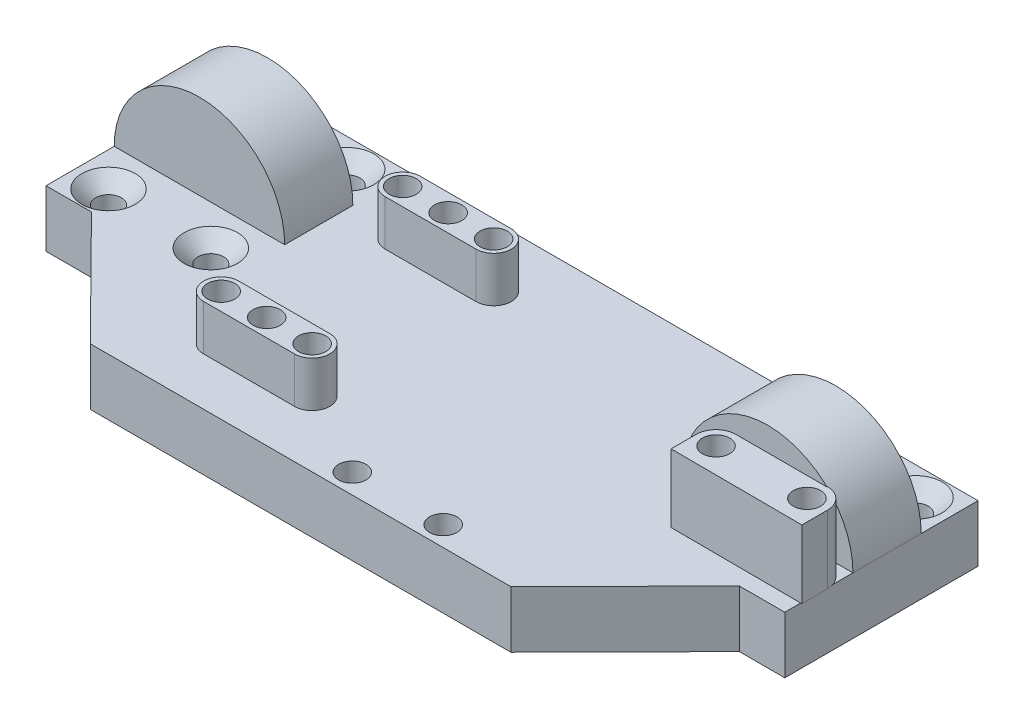
SolidWorks part; units mm, degrees
ref_plane "Front Plane" through (0, 0, 0) normal (0, 0, 1) x (1, 0, 0)
ref_plane "Top Plane" through (0, 0, 0) normal (0, 1, 0) x (1, 0, 0)
ref_plane "Right Plane" through (0, 0, 0) normal (1, 0, 0) x (0, 0, -1)
sketch "Sketch1" plane through (0, 0, 0) normal (0, 1, 0) x (1, 0, 0)
  point P0 (0, 0)
  line B0 (-64.8643, -10.474) -> (-34.8643, -10.474)
  line B1 (-34.8643, 23.526) -> (-34.8643, -10.474)
  line B2 (-64.8643, 23.526) -> (-64.8643, -10.474)
  line B3 (-64.8643, 23.526) -> (-34.8643, 23.526)
  circle B4 centre (-40.8643, -5.474) radius 2
  circle B5 centre (-58.8643, -5.474) radius 2
  circle B6 centre (-58.8643, 18.526) radius 2
  circle B7 centre (-40.8643, 18.526) radius 2
  line B8 (35.1357, -10.474) -> (65.1357, -10.474)
  line B9 (65.1357, 23.526) -> (65.1357, -10.474)
  line B10 (35.1357, 23.526) -> (35.1357, -10.474)
  line B11 (35.1357, 23.526) -> (65.1357, 23.526)
  circle B12 centre (59.1357, -5.474) radius 2
  circle B13 centre (41.1357, -5.474) radius 2
  circle B14 centre (41.1357, 18.526) radius 2
  circle B15 centre (59.1357, 18.526) radius 2
  line B16 (81.334, -15.2142) -> (81.234, -15.2142)
  line B17 (81.234, -15.2142) -> (81.234, -16.0085)
  line B18 (81.234, -16.0085) -> (81.334, -16.0085)
  line B19 (81.334, -16.0085) -> (81.334, -15.2142)
  line B20 (-6.166, 12.8273) -> (-6.266, 12.8273)
  line B21 (-6.266, 12.8273) -> (-6.266, -19.1727)
  line B22 (-6.266, -19.1727) -> (-6.166, -19.1727)
  line B23 (-6.166, -19.1727) -> (-6.166, 12.8273)
  line B24 (-6.266, -14.7727) -> (-15.766, -14.7727)
  line B25 (-15.866, -12.7727) -> (-17.766, -12.7727)
  line B26 (-17.766, -12.7727) -> (-17.766, -10.7727)
  line B27 (-17.766, -10.7727) -> (-17.766, 4.4273)
  line B28 (-17.766, 4.4273) -> (-17.766, 6.4273)
  line B29 (-15.766, 6.4273) -> (-15.766, 8.4273)
  line B30 (-15.866, 6.4273) -> (-17.766, 6.4273)
  line B31 (-6.266, 8.4273) -> (-15.766, 8.4273)
  line B32 (28.1, 4.7273) -> (33.234, 0.778)
  line B33 (33.234, 0.778) -> (33.234, -15.5313)
  line B34 (42.234, -7.5727) -> (42.234, -3.1727)
  line B35 (45.734, 0.3273) -> (61.734, 0.3273)
  line B36 (65.234, -3.1727) -> (65.234, -7.5727)
  line B37 (33.334, -7.6727) -> (73.6926, -7.6727)
  line B38 (73.6926, -7.6727) -> (81.234, -15.2142)
  line B39 (66.5698, -30.6727) -> (41.3754, -30.6727)
  line B40 (41.3754, -30.6727) -> (33.3754, -22.6727)
  line B41 (33.3754, -22.6727) -> (26.234, -22.6727)
  line B42 (25.334, -27.1727) -> (25.334, -22.7727)
  line B43 (5.734, -30.7727) -> (21.734, -30.7727)
  line B44 (2.234, -27.1727) -> (2.234, -22.7727)
  line B45 (-6.166, -22.7727) -> (1.634, -22.7727)
  line B46 (-6.166, -22.7727) -> (-6.166, -19.1727)
  line B47 (-6.166, 12.8273) -> (-6.166, 16.4273)
  line B48 (-6.166, 16.4273) -> (1.634, 16.4273)
  line B49 (1.634, 16.4273) -> (1.634, 12.8273)
  line B50 (17.7003, 12.7273) -> (27.4371, 5.3273)
  line B51 (-2.666, 12.7273) -> (17.7003, 12.7273)
  arc B52 (45.734, 0.3273) -> (42.234, -3.1727) centre (45.734, -3.1727) ccw
  arc B53 (65.334, -3.1727) -> (61.734, 0.4273) centre (61.734, -3.1727) ccw
  arc B54 (89.2916, -26.6217) -> (78.285, -15.6152) centre (77.734, -27.1727) ccw
  arc B55 (78.285, -38.7303) -> (89.2916, -27.7237) centre (77.734, -27.1727) ccw
  arc B56 (66.1764, -27.7237) -> (77.183, -38.7303) centre (77.734, -27.1727) ccw
  arc B57 (21.734, -30.7727) -> (25.334, -27.1727) centre (21.734, -27.1727) ccw
  arc B58 (2.234, -27.1727) -> (5.734, -30.6727) centre (5.734, -27.1727) ccw
  arc B59 (-6.266, -19.1727) -> (-2.666, -22.7727) centre (-2.666, -19.1727) ccw
  dimension "D1" = 130
sketch_block_instance "Block-LinearBearing-1"
sketch_block "Block-LinearBearing"
sketch_block_instance "Block-LinearBearing-2"
sketch_block_instance "Block-LARGERMOTORSIDE-1"
sketch_block "Block-LARGERMOTORSIDE"
sketch "Sketch2" plane through (0, 0, 0) normal (0, 1, 0) x (1, 0, 0)
  line L0 (35.1357, -10.474) -> (65.1357, -10.474) construction
  line L1 (65.1357, 23.526) -> (65.1357, -10.474) construction
  line L2 (35.1357, 23.526) -> (65.1357, 23.526) construction
  line L3 (-64.8643, -10.474) -> (-34.8643, -10.474) construction
  line L4 (-64.8643, 23.526) -> (-34.8643, 23.526) construction
  line L5 (-64.8643, 23.526) -> (-64.8643, -10.474) construction
  line L6 (35.1357, -10.474) -> (65.1357, -10.474)
  line L7 (65.1357, 23.526) -> (65.1357, -10.474)
  line L8 (35.1357, 23.526) -> (65.1357, 23.526)
  line L9 (-64.8643, -10.474) -> (-34.8643, -10.474)
  line L10 (-64.8643, 23.526) -> (-34.8643, 23.526)
  line L11 (-64.8643, 23.526) -> (-64.8643, -10.474)
  line L12 (-34.8643, 23.526) -> (35.1357, 23.526)
  line L13 (-34.8643, -10.474) -> (35.1357, -10.474)
  line L14 (-17.766, -12.7727) -> (-17.766, -30.6727)
  line L15 (-17.766, -30.6727) -> (37.1357, -30.6727)
  line L16 (66.5698, -30.6727) -> (41.3754, -30.6727) construction
  line L17 (-17.766, -12.7727) -> (-17.766, -10.7727)
  line L18 (37.1357, -30.6727) -> (57.1357, -10.474)
  line L19 (-56.8643, -10.474) -> (-36.8643, -30.6727)
  line L20 (-36.8643, -30.6727) -> (-17.766, -30.6727)
  point P20 (41.3754, -30.6727)
  point P21 (0, 0)
  dimension "D1" = 8
  dimension "D2" = 8
  dimension "D3" = 20
  dimension "D4" = 20
extrude "Boss-Extrude1" add sketch "Sketch2" along normal blind 10 contours L9 L13 L6 L7 L8 L12 L10 L11
sketch "Sketch3" plane through (0, 0, 0) normal (0, -1, 0) x (1, 0, 0)
  line L0 (-34.8643, 10.474) -> (35.1357, 10.474) construction
  line L1 (35.1357, 10.474) -> (65.1357, 10.474) construction
  line L2 (37.1357, 30.6727) -> (57.1357, 10.474) construction
  line L3 (-17.766, 10.7727) -> (-17.766, -4.4273) construction
  line L4 (-17.766, 12.7727) -> (-17.766, 10.7727) construction
  line L5 (-17.766, 30.6727) -> (37.1357, 30.6727) construction
  line L6 (-17.766, 12.7727) -> (-17.766, 30.6727) construction
  line L7 (-17.766, 10.474) -> (35.1357, 10.474)
  line L8 (35.1357, 10.474) -> (57.1357, 10.474)
  line L9 (37.1357, 30.6727) -> (57.1357, 10.474)
  line L10 (-17.766, 10.7727) -> (-17.766, 10.474)
  line L11 (-17.766, 12.7727) -> (-17.766, 10.7727)
  line L12 (-17.766, 30.6727) -> (37.1357, 30.6727)
  line L13 (-17.766, 12.7727) -> (-17.766, 30.6727)
  line L14 (-56.8643, 10.474) -> (-36.8643, 30.6727) construction
  line L15 (-56.8643, 10.474) -> (-36.8643, 30.6727)
  line L16 (-36.8643, 30.6727) -> (-17.766, 30.6727) construction
  line L17 (-36.8643, 30.6727) -> (-17.766, 30.6727)
  line L18 (-64.8643, 10.474) -> (-34.8643, 10.474) construction
  line L19 (-56.8643, 10.474) -> (-34.8643, 10.474)
  line L20 (-34.8643, 10.474) -> (35.1357, 10.474)
  line M1 (65.1357, 10.474) -> (-64.8643, 10.474)
extrude "Boss-Extrude2" add sketch "Sketch3" against normal blind 10 contours L17 L15 L10 L11 L13 M1 | L13 L11 L10 L9 L12 M1
sketch "Sketch4" plane through (0, 10, 0) normal (0, 1, 0) x (1, 0, 0)
  line L0 (65.234, -3.1727) -> (65.234, -7.5727) construction
  line L1 (33.334, -7.6727) -> (73.6926, -7.6727) construction
  line L2 (42.234, -7.5727) -> (42.234, -3.1727) construction
  line L3 (45.734, 0.3273) -> (61.734, 0.3273) construction
  line L4 (65.234, -3.1727) -> (65.234, -7.5727)
  line L5 (33.334, -7.6727) -> (73.6926, -7.6727)
  line L6 (42.234, -7.5727) -> (42.234, -3.1727)
  line L7 (45.734, 0.3273) -> (61.734, 0.3273)
  circle A0 centre (5.734, -27.1727) radius 2.4
  circle A1 centre (21.734, -27.1727) radius 2.4
  circle A2 centre (45.734, -3.1727) radius 2.4
  circle A3 centre (61.734, -3.1727) radius 2.4
  arc A4 (65.334, -3.1727) -> (61.734, 0.4273) centre (61.734, -3.1727) ccw construction
  arc A5 (45.734, 0.3273) -> (42.234, -3.1727) centre (45.734, -3.1727) ccw construction
  arc A6 (65.334, -3.1727) -> (61.734, 0.4273) centre (61.734, -3.1727) ccw
  arc A7 (45.734, 0.3273) -> (42.234, -3.1727) centre (45.734, -3.1727) ccw
  dimension "D1" = 4.8
extrude "Cut-Extrude1" cut sketch "Sketch4" against normal blind 8 contours A0 | A1
sketch "Sketch5" plane through (0, 10, 0) normal (0, 1, 0) x (1, 0, 0)
  line L1 (42.234, -7.5727) -> (42.234, -3.1727) construction
  line L2 (45.734, 0.3273) -> (61.734, 0.3273) construction
  line L3 (42.234, -7.5727) -> (65.334, -7.6727)
  line L4 (42.234, -7.5727) -> (42.234, -3.1727)
  line L5 (45.734, 0.3273) -> (61.734, 0.3273)
  line L6 (65.334, -3.1727) -> (65.334, -7.6727)
  line L7 (61.734, 0.4273) -> (61.734, 0.3273)
  arc A0 (65.334, -3.1727) -> (61.734, 0.4273) centre (61.734, -3.1727) ccw construction
  arc A1 (45.734, 0.3273) -> (42.234, -3.1727) centre (45.734, -3.1727) ccw construction
  arc A2 (65.334, -3.1727) -> (61.734, 0.4273) centre (61.734, -3.1727) ccw
  arc A3 (45.734, 0.3273) -> (42.234, -3.1727) centre (45.734, -3.1727) ccw
  circle A4 centre (61.734, -3.1727) radius 2.4 construction
  circle A5 centre (61.734, -3.1727) radius 2.4
  circle A6 centre (45.734, -3.1727) radius 2.4 construction
  circle A7 centre (45.734, -3.1727) radius 2.4
extrude "Boss-Extrude3" add sketch "Sketch5" along normal blind 12
hole_wizard "CSK for M4 Flat Head Machine Screw1" positions "Sketch6" profile "Sketch7" countersink size "M4" standard "ANSI Metric" end condition up to next
sketch "Sketch6" plane through (0, 10, 0) normal (0, 1, 0) x (1, 0, 0)
  point P0 (-58.8643, 18.526)
  point P3 (-40.8643, 18.526)
  point P6 (-58.8643, -5.474)
  point P9 (-40.8643, -5.474)
  point P12 (41.1357, 18.526)
  point P15 (59.1357, 18.526)
sketch "Sketch7" plane through (-58.8643, 10, -18.526) normal (1, 0, 0) x (0, 0, 1)
  line L0 (0, 0) -> (0, 10)
  line L1 (0, 10) -> (2.25, 10)
  line L2 (2.25, 10) -> (2.25, 2.45)
  line L3 (2.25, 2.45) -> (4.7, 0)
  line L5 (4.7, 0) -> (0, 0)
  line L6 (-2.25, 2.45) -> (-4.7, 0) construction
  line L11 (0, -6.35) -> (0, 107.95) construction
  dimension "Thru Hole Dia." = 4.5
  dimension "Thru Hole Depth" = 10
  dimension "Near C'Sink Dia." = 9.4
  dimension "Near C'Sink Angle" = 90
sketch "Sketch9" plane through (0, 10, 0) normal (0, 1, 0) x (1, 0, 0)
  line L0 (-6.266, 12.8273) -> (-6.266, -19.1727) construction
  line L1 (-6.266, -14.7727) -> (-15.766, -14.7727) construction
  line L2 (-17.766, -3.1727) -> (-6.266, -3.1727) construction
  line L3 (-17.766, -10.7727) -> (-17.766, 4.4273) construction
  line B0 (-25.366, -16.0427) -> (-9.366, -16.0427)
  line B1 (-25.366, -22.2427) -> (-9.366, -22.2427)
  circle B2 centre (-9.366, -19.1427) radius 2.4
  circle B3 centre (-17.366, -19.1427) radius 2.4
  circle B4 centre (-25.366, -19.1427) radius 2.4
  arc B5 (-25.366, -16.0427) -> (-25.366, -22.2427) centre (-25.366, -19.1427) ccw
  arc B6 (-9.366, -22.2427) -> (-9.366, -16.0427) centre (-9.366, -19.1427) ccw
  line B7 (-25.366, 9.6973) -> (-9.366, 9.6973)
  line B8 (-25.366, 15.8973) -> (-9.366, 15.8973)
  circle B9 centre (-9.366, 12.7973) radius 2.4
  circle B10 centre (-17.366, 12.7973) radius 2.4
  circle B11 centre (-25.366, 12.7973) radius 2.4
  arc B12 (-25.366, 9.6973) -> (-25.366, 15.8973) centre (-25.366, 12.7973) cw
  arc B13 (-9.366, 15.8973) -> (-9.366, 9.6973) centre (-9.366, 12.7973) cw
  dimension "D1" = 1.27
sketch_block_instance "Block-3HolePiece-1"
sketch_block "Block1"
sketch_block_instance "Block1-2"
sketch "Sketch10" plane through (0, 10, 0) normal (0, 1, 0) x (1, 0, 0)
  line L0 (-25.366, -16.0427) -> (-9.366, -16.0427) construction
  line L1 (-25.366, -16.0427) -> (-9.366, -16.0427)
  line L2 (-25.366, 9.6973) -> (-9.366, 9.6973) construction
  line L3 (-25.366, 15.8973) -> (-9.366, 15.8973) construction
  line L4 (-25.366, -22.2427) -> (-9.366, -22.2427) construction
  line L5 (-25.366, 9.6973) -> (-9.366, 9.6973)
  line L6 (-25.366, 15.8973) -> (-9.366, 15.8973)
  line L7 (-25.366, -22.2427) -> (-9.366, -22.2427)
  arc A0 (-9.366, 9.6973) -> (-9.366, 15.8973) centre (-9.366, 12.7973) ccw construction
  circle A1 centre (-9.366, 12.7973) radius 2.4 construction
  circle A2 centre (-17.366, 12.7973) radius 2.4 construction
  circle A3 centre (-25.366, 12.7973) radius 2.4 construction
  arc A4 (-25.366, 15.8973) -> (-25.366, 9.6973) centre (-25.366, 12.7973) ccw construction
  circle A5 centre (-25.366, -19.1427) radius 2.4 construction
  circle A6 centre (-17.366, -19.1427) radius 2.4 construction
  circle A7 centre (-9.366, -19.1427) radius 2.4 construction
  arc A8 (-9.366, -22.2427) -> (-9.366, -16.0427) centre (-9.366, -19.1427) ccw construction
  arc A9 (-25.366, -16.0427) -> (-25.366, -22.2427) centre (-25.366, -19.1427) ccw construction
  arc A10 (-9.366, 9.6973) -> (-9.366, 15.8973) centre (-9.366, 12.7973) ccw
  circle A11 centre (-9.366, 12.7973) radius 2.4
  circle A12 centre (-17.366, 12.7973) radius 2.4
  circle A13 centre (-25.366, 12.7973) radius 2.4
  arc A14 (-25.366, 15.8973) -> (-25.366, 9.6973) centre (-25.366, 12.7973) ccw
  circle A15 centre (-25.366, -19.1427) radius 2.4
  circle A16 centre (-17.366, -19.1427) radius 2.4
  circle A17 centre (-9.366, -19.1427) radius 2.4
  arc A18 (-9.366, -22.2427) -> (-9.366, -16.0427) centre (-9.366, -19.1427) ccw
  arc A19 (-25.366, -16.0427) -> (-25.366, -22.2427) centre (-25.366, -19.1427) ccw
extrude "Boss-Extrude4" add sketch "Sketch10" along normal blind 8
ref_plane "Plane1" through (0, 0, -13.526) normal (0, 0, -1) x (-1, 0, 0)
sketch "Sketch11" plane through (0, 0, -13.526) normal (0, 0, -1) x (-1, 0, 0)
  line L0 (-50.1357, 0) -> (-50.1357, 16.7) construction
  line L1 (-37.1357, 0) -> (-57.1357, 0) construction
  line L2 (-65.1357, 10) -> (-65.1357, 0) construction
  line L3 (-33.334, 10) -> (-73.6926, 10) construction
  line L4 (-33.334, 10) -> (-65.1357, 10)
  circle A0 centre (-50.1357, 16.7) radius 4
  arc A1 (-35.1357, 10) -> (-65.1357, 10) centre (-50.1357, 10) ccw
  point P9 (0, 0)
  dimension "D3" = 8
  dimension "D4" = 30
  dimension "D1" = 15
  dimension "D2" = 16.7
extrude "Boss-Extrude5" add sketch "Sketch11" against normal blind 12
ref_plane "Plane2" through (0.1357, 0, 0) normal (1, 0, 0) x (0, 0, -1)
sketch "Sketch12" plane through (0, 0, -1.526) normal (0, 0, 1) x (1, 0, 0)
  circle A0 centre (50.1357, 16.7) radius 4 construction
  circle A1 centre (50.1357, 16.7) radius 4
extrude "Boss-Extrude6" add sketch "Sketch12" against normal blind 4
mirror "Mirror1" about plane through (0.1357, 0, 0) normal (1, 0, 0) of "Boss-Extrude6", "Boss-Extrude5"
